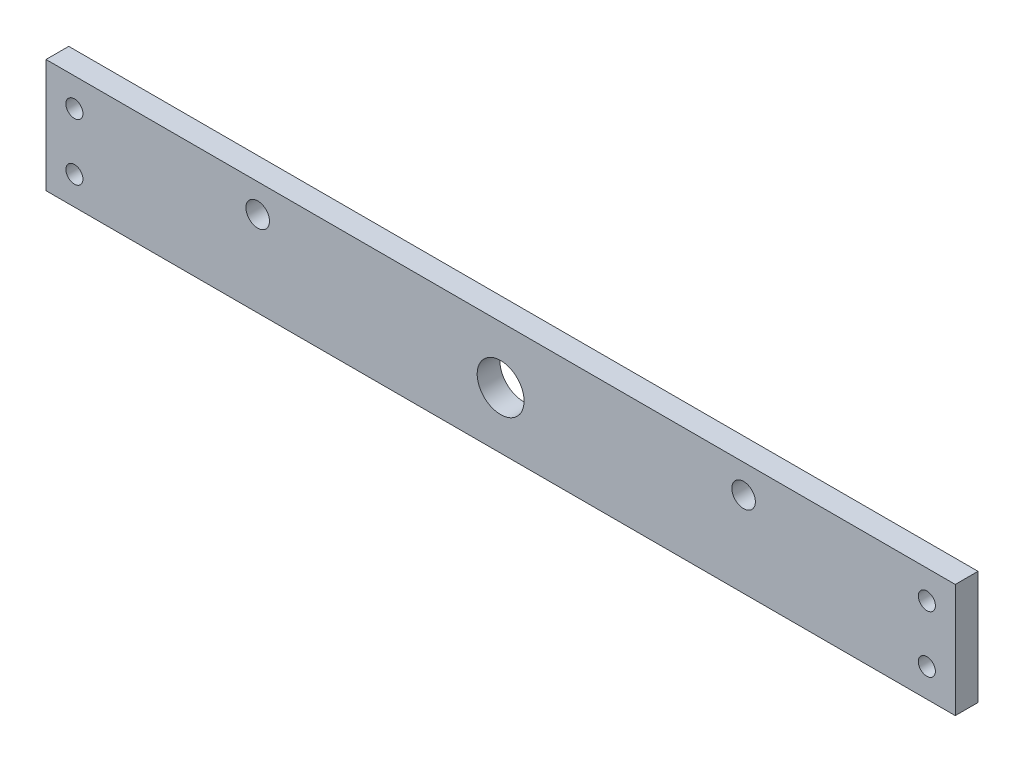
SolidWorks part; units mm, degrees
ref_plane "Front Plane" through (0, 0, 0) normal (0, 0, 1) x (1, 0, 0)
ref_plane "Top Plane" through (0, 0, 0) normal (0, 1, 0) x (1, 0, 0)
ref_plane "Right Plane" through (0, 0, 0) normal (1, 0, 0) x (0, 0, -1)
sketch "Sketch1" plane through (0, 0, 0) normal (0, 0, 1) x (1, 0, 0)
  line L1 (-160, -20) -> (160, -20)
  line L2 (-160, -20) -> (-160, 20)
  line L3 (-160, 20) -> (160, 20)
  line L4 (160, -20) -> (160, 20)
  line L5 (-160, -20) -> (160, 20) construction
  line L6 (-160, 20) -> (160, -20) construction
  point P0 (0, 0)
  dimension "D1" = 320
  dimension "D2" = 40
extrude "Boss-Extrude1" add sketch "Sketch1" along normal blind 8
sketch "Sketch2" plane through (0, 0, 8) normal (0, 0, 1) x (1, 0, 0)
  line L0 (0, 20) -> (0, -20) construction
  line L1 (160, 20) -> (-160, 20) construction
  line L2 (-160, -20) -> (160, -20) construction
  line L3 (-160, 0) -> (160, 0) construction
  line L4 (-160, 20) -> (-160, -20) construction
  line L5 (160, -20) -> (160, 20) construction
  circle A0 centre (-150, 10) radius 3
  circle A1 centre (-150, -10) radius 3
  circle A2 centre (150, -10) radius 3
  circle A3 centre (150, 10) radius 3
  dimension "D1" = 10
  dimension "D2" = 10
  dimension "D3" = 6
extrude "Cut-Extrude1" cut sketch "Sketch2" against normal up to next
sketch "Sketch3" plane through (0, 0, 8) normal (0, 0, 1) x (1, 0, 0)
  line L0 (0, 20) -> (0, -20) construction
  line L1 (160, 20) -> (-160, 20) construction
  line L2 (-160, -20) -> (160, -20) construction
  line L3 (-150, 10) -> (150, 10) construction
  circle A0 centre (-85.5, 10) radius 4.15
  circle A1 centre (85.5, 10) radius 4.15
  circle A2 centre (0, 0) radius 8.25
  dimension "D1" = 8.3
  dimension "D2" = 85.5
  dimension "D3" = 16.5
extrude "Cut-Extrude2" cut sketch "Sketch3" against normal up to next
